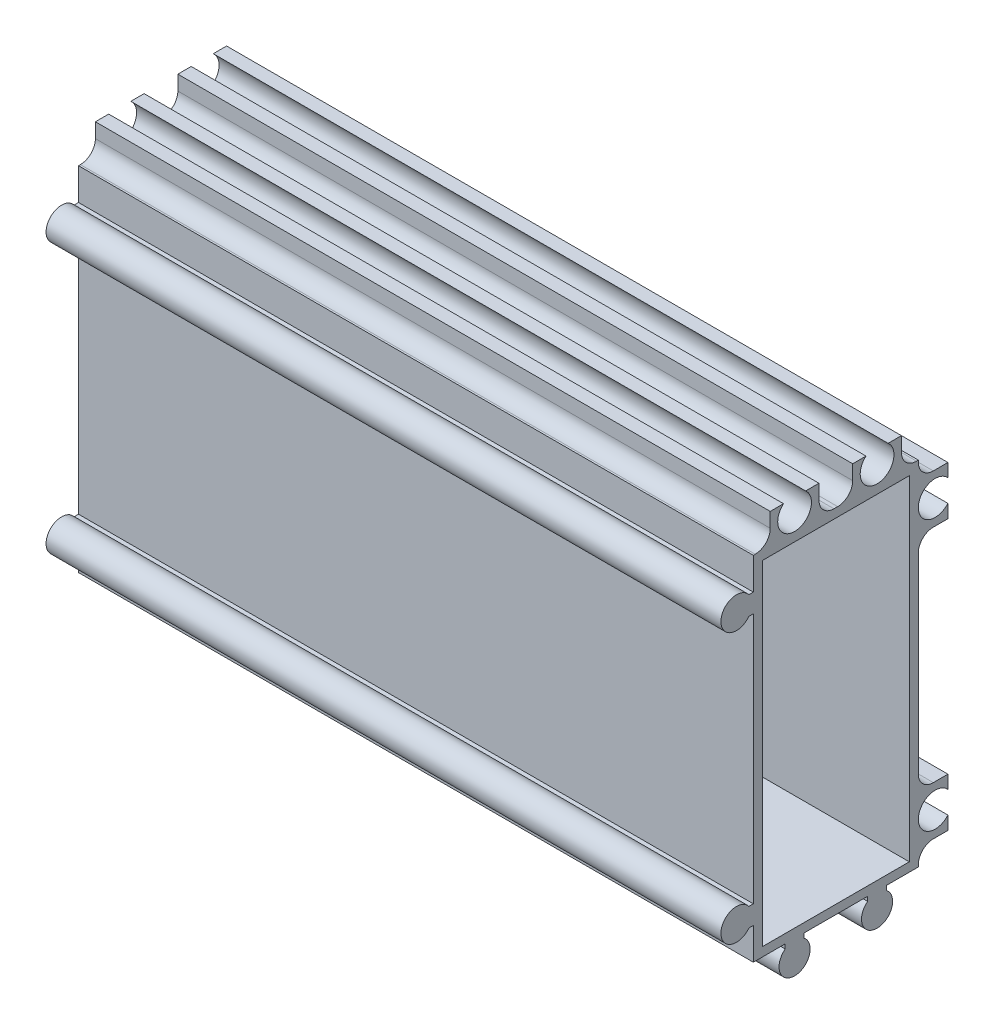
SolidWorks part; units mm, degrees
ref_plane "Спереди" through (0, 0, 0) normal (0, 0, 1) x (1, 0, 0)
ref_plane "Сверху" through (0, 0, 0) normal (0, 1, 0) x (1, 0, 0)
ref_plane "Справа" through (0, 0, 0) normal (1, 0, 0) x (0, 0, -1)
ref_plane "Плоскость4" through (90, 0, 0) normal (1, 0, 0) x (0, 0, -1)
sketch "Эскиз1" plane through (90, 0, 0) normal (1, 0, 0) x (0, 0, -1)
  line L0 (6.75, -24.0938) -> (6.75, 19.25)
  line L1 (6.75, 19.25) -> (-11.5938, 19.25)
  line L2 (-11.5938, 16.75) -> (-11, 16.75)
  line L3 (-11, 16.75) -> (-11, -16.75)
  line L4 (-11, -16.75) -> (-11.5938, -16.75)
  line L5 (-11.5938, -19.25) -> (-11, -19.25)
  line L6 (-11, -19.25) -> (-11, -23.5)
  line L7 (-11, -23.5) -> (-6.75, -23.5)
  line L8 (-6.75, -23.5) -> (-6.75, -24.0938)
  line L9 (-4.25, -24.0938) -> (-4.25, -23.5)
  line L10 (-4.25, -23.5) -> (4.25, -23.5)
  line L11 (4.25, -23.5) -> (4.25, -24.0938)
  arc A0 (-11.5938, 19.25) -> (-11.5938, 16.75) centre (-13.25, 18) ccw
  arc A1 (-11.5938, -16.75) -> (-11.5938, -19.25) centre (-13.25, -18) ccw
  arc A2 (-6.75, -24.0938) -> (-4.25, -24.0938) centre (-5.5, -25.75) ccw
  arc A3 (4.25, -24.0938) -> (6.75, -24.0938) centre (5.5, -25.75) ccw
extrude "Бобышка-Вытянуть1" add sketch "Эскиз1" against normal blind 90
sketch "Эскиз2" plane through (0, 19.25, 0) normal (0, 1, 0) x (-1, 0, 0)
  line L0 (-90, -6.75) -> (-90, 11)
  line L1 (-90, 11) -> (0, 11)
  line L2 (0, 11) -> (0, -6.75)
  line L3 (0, -6.75) -> (-90, -6.75)
extrude "Бобышка-Вытянуть2" add sketch "Эскиз2" along normal blind 8.2
sketch "Эскиз3" plane through (0, 0, -6.75) normal (0, 0, -1) x (-1, 0, 0)
  line L0 (0, -23.5) -> (-90, -23.5)
  line L1 (-90, -23.5) -> (-90, 27.45)
  line L2 (-90, 27.45) -> (0, 27.45)
  line L3 (0, 27.45) -> (0, -23.5)
extrude "Бобышка-Вытянуть3" add sketch "Эскиз3" along normal blind 8.2
sketch "Эскиз4" plane through (0, 0, 0) normal (-1, 0, 0) x (0, 0, 1)
  line L0 (-14.95, -14.75) -> (-11, -14.75)
  line L1 (-11, -14.75) -> (-11, 14.75)
  line L2 (-11, 14.75) -> (-14.95, 14.75)
  line L3 (-14.95, 14.75) -> (-14.95, -14.75)
extrude "Вырез-Вытянуть1" cut sketch "Эскиз4" against normal through all
sketch "Эскиз5" plane through (0, 0, 0) normal (-1, 0, 0) x (0, 0, 1)
  line L0 (-14.95, 27.45) -> (-14.95, 21.25)
  line L1 (-14.95, 21.25) -> (-11, 21.25)
  line L2 (-11, 21.25) -> (-11, 27.45)
  line L3 (-11, 27.45) -> (-14.95, 27.45)
extrude "Вырез-Вытянуть2" cut sketch "Эскиз5" against normal through all
sketch "Эскиз6" plane through (0, 0, 0) normal (-1, 0, 0) x (0, 0, 1)
  line L0 (-11, 27.45) -> (-11, 23.5)
  line L1 (-11, 23.5) -> (-8.75, 23.5)
  line L2 (-8.75, 23.5) -> (-8.75, 27.45)
  line L3 (-8.75, 27.45) -> (-11, 27.45)
extrude "Вырез-Вытянуть3" cut sketch "Эскиз6" against normal through all
sketch "Эскиз7" plane through (0, 0, 0) normal (-1, 0, 0) x (0, 0, 1)
  line L0 (-2.25, 27.45) -> (-2.25, 23.5)
  line L1 (-2.25, 23.5) -> (2.25, 23.5)
  line L2 (2.25, 23.5) -> (2.25, 27.45)
  line L3 (2.25, 27.45) -> (-2.25, 27.45)
extrude "Вырез-Вытянуть4" cut sketch "Эскиз7" against normal through all
sketch "Эскиз8" plane through (0, 0, 0) normal (-1, 0, 0) x (0, 0, 1)
  line L0 (11, 27.45) -> (8.75, 27.45)
  line L1 (8.75, 27.45) -> (8.75, 23.5)
  line L2 (8.75, 23.5) -> (11, 23.5)
  line L3 (11, 23.5) -> (11, 27.45)
extrude "Вырез-Вытянуть5" cut sketch "Эскиз8" against normal through all
sketch "Эскиз9" plane through (0, 0, 0) normal (-1, 0, 0) x (0, 0, 1)
  line L0 (-14.95, -23.5) -> (-11, -23.5)
  line L1 (-11, -23.5) -> (-11, -21.25)
  line L2 (-11, -21.25) -> (-14.95, -21.25)
  line L3 (-14.95, -21.25) -> (-14.95, -23.5)
extrude "Вырез-Вытянуть6" cut sketch "Эскиз9" against normal through all
sketch "Эскиз10" plane through (90, 0, 0) normal (1, 0, 0) x (0, 0, -1)
  line L0 (9.8, 22.3) -> (-9.8, 22.3)
  line L1 (-9.8, 22.3) -> (-9.8, -22.3)
  line L2 (-9.8, -22.3) -> (9.8, -22.3)
  line L3 (9.8, -22.3) -> (9.8, 22.3)
  line L4 (-11, 16.75) -> (-11, -16.75) construction
  line L8 (11, -14.75) -> (11, 14.75) construction
  line L9 (2.25, 23.5) -> (-2.25, 23.5) construction
  line L10 (-4.25, -23.5) -> (4.25, -23.5) construction
  dimension "D1" = 1.2
  dimension "D2" = 1.2
  dimension "D3" = 1.2
  dimension "D4" = 1.2
extrude "Вырез-Вытянуть7" cut sketch "Эскиз10" against normal blind 86.2
hole_wizard "Диаметр отверстия Ø2.5 (2.5)1" positions "Эскиз12" profile "Эскиз11" hole size "Ø2.5" standard "Ansi Metric"
sketch "Эскиз12" plane through (90, 0, 0) normal (1, 0, 0) x (0, 0, -1)
  point P0 (5.5, -25.75)
  point P1 (-13.25, -18)
  point P2 (-5.5, -25.75)
  point P3 (-13.25, 18)
sketch "Эскиз11" plane through (90, -25.75, -5.5) normal (0, 1, 0) x (0, 0, -1)
  line L0 (0, 0) -> (0, 90)
  line L1 (0, 90) -> (1.25, 90)
  line L2 (1.25, 90) -> (1.25, 0)
  line L5 (1.25, 0) -> (0, 0)
  line L11 (0, -6.35) -> (0, 107.95) construction
  dimension "Диаметр сквозного отверстия" = 2.5
  dimension "Глубина сквозного отверстия" = 90
hole_wizard "Диаметр отверстия Ø4.5 (4.5)1" positions "Эскиз14" profile "Эскиз13" hole size "Ø4.5" standard "Ansi Metric"
sketch "Эскиз14" plane through (0, 0, 0) normal (-1, 0, 0) x (0, 0, 1)
  point P0 (-13.25, -18)
  point P1 (-13.25, 18)
  point P2 (-5.5, 25.75)
  point P3 (5.5, 25.75)
sketch "Эскиз13" plane through (0, -18, -13.25) normal (0, 1, 0) x (0, 0, 1)
  line L0 (0, 0) -> (0, 90)
  line L1 (0, 90) -> (2.25, 90)
  line L2 (2.25, 90) -> (2.25, 0)
  line L5 (2.25, 0) -> (0, 0)
  line L11 (0, -6.35) -> (0, 107.95) construction
  dimension "Диаметр сквозного отверстия" = 4.5
  dimension "Глубина сквозного отверстия" = 90
hole_wizard "Диаметр отверстия Ø8.3 (8.3)1" [suppressed] positions "Эскиз16" profile "Эскиз15" hole size "Ø8.3" standard "Ansi Metric"
sketch "Эскиз16" plane through (0, 0, 0) normal (-1, 0, 0) x (0, 0, 1)
  point P0 (0, 0)
sketch "Эскиз15" plane through (0, 0, 0) normal (0, 1, 0) x (0, 0, 1)
  line L0 (0, 0) -> (0, 3.2)
  line L1 (0, 3.2) -> (4.15, 3.2)
  line L2 (4.15, 3.2) -> (4.15, 0)
  line L5 (4.15, 0) -> (0, 0)
  line L10 (0, 3.2) -> (-4.15, 3.2) construction
  line L11 (0, -6.35) -> (0, 107.95) construction
  dimension "Диаметр отверстия" = 8.3
  dimension "Глубина отверстия" = 3.2
  dimension "Угол заточки сверла" = 180
fillet "Скругление1" radius 2 1 edges at (45, 23.5, 8.75)
fillet "Скругление2" radius 2 7 edges at (45, -21.25, -11) (45, -14.75, -11) (45, 14.75, -11) (45, 21.25, -11) (45, 23.5, -8.75) (45, 23.5, -2.25) (45, 23.5, 2.25)
sketch "Эскиз17" plane through (90, 0, 0) normal (1, 0, 0) x (0, 0, -1)
  circle A0 centre (5.5, -25.75) radius 1.25 construction
  circle A1 centre (-5.5, -25.75) radius 1.25 construction
  circle A2 centre (-13.25, -18) radius 1.25 construction
  circle A3 centre (-13.25, 18) radius 1.25 construction
  circle A4 centre (5.5, -25.75) radius 1.25
  circle A5 centre (-5.5, -25.75) radius 1.25
  circle A6 centre (-13.25, -18) radius 1.25
  circle A7 centre (-13.25, 18) radius 1.25
extrude "Бобышка-Вытянуть4" add sketch "Эскиз17" against normal blind 90
sketch "Эскиз18" [suppressed] plane through (0, 0, 0) normal (-1, 0, 0) x (0, 0, 1)
  circle A0 centre (0, 0) radius 4.15 construction
  circle A1 centre (0, 0) radius 4.15
extrude "Вырез-Вытянуть8" [suppressed] cut sketch "Эскиз18" against normal blind 100
equation "\"D2@Эскиз10\"=\"D1@Эскиз10\""
equation "\"D3@Эскиз10\"=\"D1@Эскиз10\""
equation "\"D4@Эскиз10\"=\"D1@Эскиз10\""
